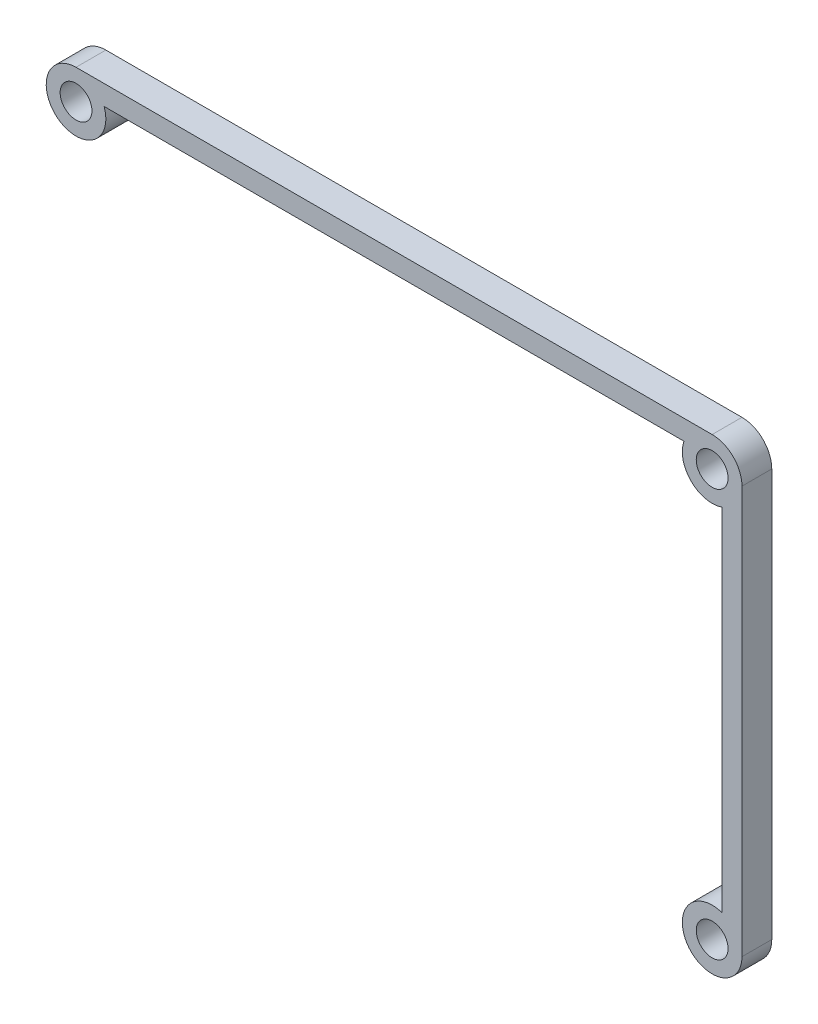
SolidWorks part; units mm, degrees
ref_plane "Plano frontal" through (0, 0, 0) normal (0, 0, 1) x (1, 0, 0)
ref_plane "Plano superior" through (0, 0, 0) normal (0, 1, 0) x (1, 0, 0)
ref_plane "Plano direito" through (0, 0, 0) normal (1, 0, 0) x (0, 0, -1)
sketch "Esboço1" plane through (0, 0, 0) normal (0, 0, 1) x (1, 0, 0)
  line L0 (0, 6.9538) -> (0, 0) construction
  line L1 (0, 0) -> (6.3156, 0) construction
  line L2 (35, 20.5) -> (35, -20.5)
  line L3 (-32, 23.5) -> (32, 23.5)
  line L4 (-29.1716, 21.5) -> (29.1716, 21.5)
  line L5 (33, 17.6716) -> (33, -17.6716)
  circle A0 centre (-32, 20.5) radius 1.6
  circle A1 centre (32, 20.5) radius 1.6
  circle A2 centre (32, -20.5) radius 1.6
  arc A3 (-32, 23.5) -> (-29.1716, 21.5) centre (-32, 20.5) ccw
  arc A4 (32, 23.5) -> (35, 20.5) centre (32, 20.5) cw
  arc A5 (33, -17.6716) -> (35, -20.5) centre (32, -20.5) ccw
  arc A6 (33, 17.6716) -> (29.1716, 21.5) centre (32, 20.5) cw
  dimension "D1" = 3.2
  dimension "D2" = 6
  dimension "D3" = 64
  dimension "D4" = 41
  dimension "D5" = 2
  dimension "D6" = 2
extrude "Ressalto-extrusão1" add sketch "Esboço1" along normal blind 3
equation "\"D6@Esboço1\"=\"D5@Esboço1\""
